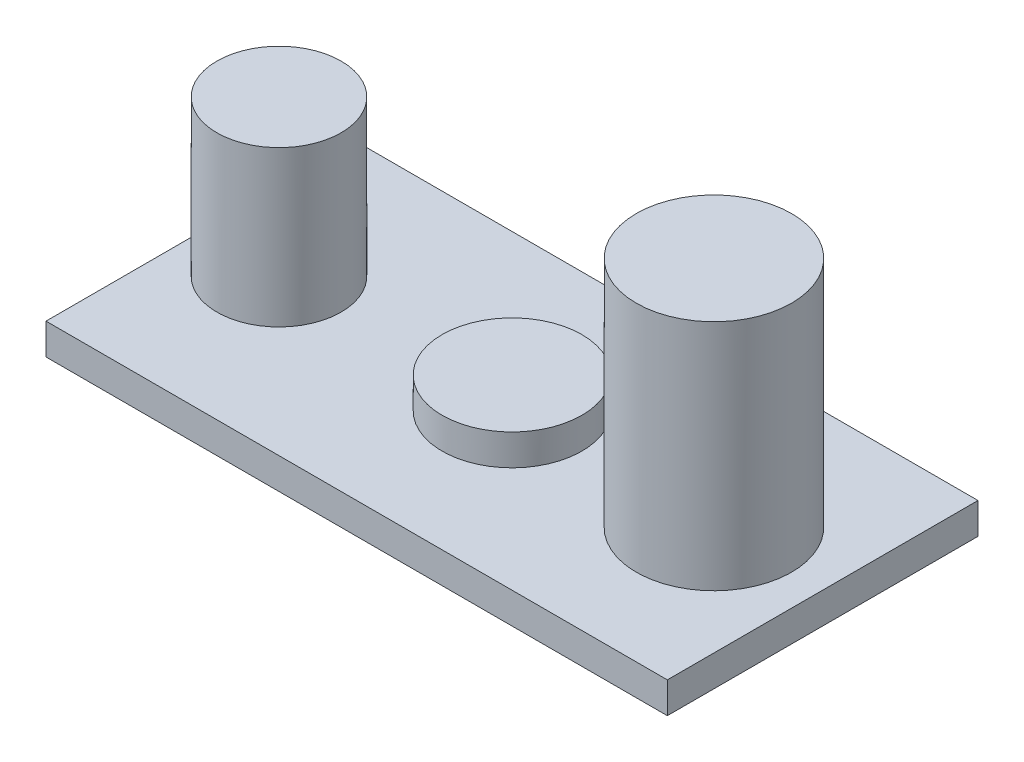
SolidWorks part; units mm, degrees
ref_plane "Front Plane" through (0, 0, 0) normal (0, 0, 1) x (1, 0, 0)
ref_plane "Top Plane" through (0, 0, 0) normal (0, 1, 0) x (1, 0, 0)
ref_plane "Right Plane" through (0, 0, 0) normal (1, 0, 0) x (0, 0, -1)
sketch "Sketch1" plane through (0, 0, 0) normal (0, 1, 0) x (1, 0, 0)
  line L0 (0, 25) -> (100, 25) construction
  line L1 (0, 0) -> (100, 0)
  line L2 (0, 0) -> (0, 50)
  line L3 (0, 50) -> (100, 50)
  line L4 (100, 0) -> (100, 50)
  line L5 (50, 0) -> (50, 50) construction
  dimension "D1" = 50
  dimension "D2" = 100
extrude "Boss-Extrude1" add sketch "Sketch1" along normal blind 5
sketch "Sketch3" plane through (0, 5, 0) normal (0, 1, 0) x (1, 0, 0)
  line L0 (0, 25) -> (100, 25) construction
  line L1 (0, 50) -> (0, 0) construction
  line L2 (100, 0) -> (100, 50) construction
  line L3 (50, 0) -> (50, 50) construction
  line L4 (0, 0) -> (100, 0) construction
  line L5 (100, 50) -> (0, 50) construction
  circle A0 centre (12.5, 25) radius 10
  dimension "D2" = 20
  dimension "D1" = 12.5
extrude "Boss-Extrude2" add sketch "Sketch3" along normal blind 25
sketch "Sketch4" plane through (0, 5, 0) normal (0, 1, 0) x (1, 0, 0)
  line L0 (0, 25) -> (100, 25) construction
  line L1 (0, 50) -> (0, 0) construction
  line L2 (100, 0) -> (100, 50) construction
  line L3 (50, 50) -> (50, 0) construction
  line L4 (100, 50) -> (0, 50) construction
  line L5 (0, 0) -> (100, 0) construction
  circle A0 centre (50, 25) radius 11.25
  dimension "D1" = 22.5
extrude "Boss-Extrude3" add sketch "Sketch4" along normal blind 5 contours A0
sketch "Sketch5" plane through (0, 5, 0) normal (0, 1, 0) x (1, 0, 0)
  line L0 (0, 25) -> (100, 25) construction
  line L1 (0, 50) -> (0, 0) construction
  line L2 (100, 0) -> (100, 50) construction
  line L3 (50, 50) -> (50, 0) construction
  line L4 (100, 50) -> (0, 50) construction
  line L5 (0, 0) -> (100, 0) construction
  circle A0 centre (82.5, 25) radius 12.5
  dimension "D2" = 25
  dimension "D1" = 17.5
extrude "Boss-Extrude4" add sketch "Sketch5" along normal blind 37.5
equation "\"box_height\"= 50"
equation "\"box_width\"= \"box_height\" * 2"
equation "\"C1_diam\"= \"box_width\" / 5"
equation "\"C2_diam\"= \"box_width\" / 4"
equation "\"C3_diam\"= ( \"C1_diam\" + \"C2_diam\" ) / 2"
equation "\"C1_dist\"= \"box_width\" / 8"
equation "\"C2_dist\"= ( \"C2_diam\" / 2 ) + 5"
equation "\"D1@Sketch1\"=\"box_height\""
equation "\"D2@Sketch1\"=\"box_width\""
equation "\"C1_height\"= \"C2_diam\""
equation "\"C2_height\"= \"C2_diam\" * 1.5"
equation "\"C3_height\"= \"Extrude\""
equation "\"Extrude\"= \"box_height\" / 10"
equation "\"D1@Boss-Extrude1\"=\"Extrude\""
equation "\"D1@Sketch3\"=\"C1_dist\""
equation "\"D2@Sketch3\"=\"C1_diam\""
equation "\"D1@Boss-Extrude2\"=\"C1_height\""
equation "\"D1@Sketch4\"=\"C3_diam\""
equation "\"D1@Boss-Extrude3\"=\"C3_height\""
equation "\"D1@Sketch5\"=\"C2_dist\""
equation "\"D2@Sketch5\"=\"C2_diam\""
equation "\"D1@Boss-Extrude4\"=\"C2_height\""
